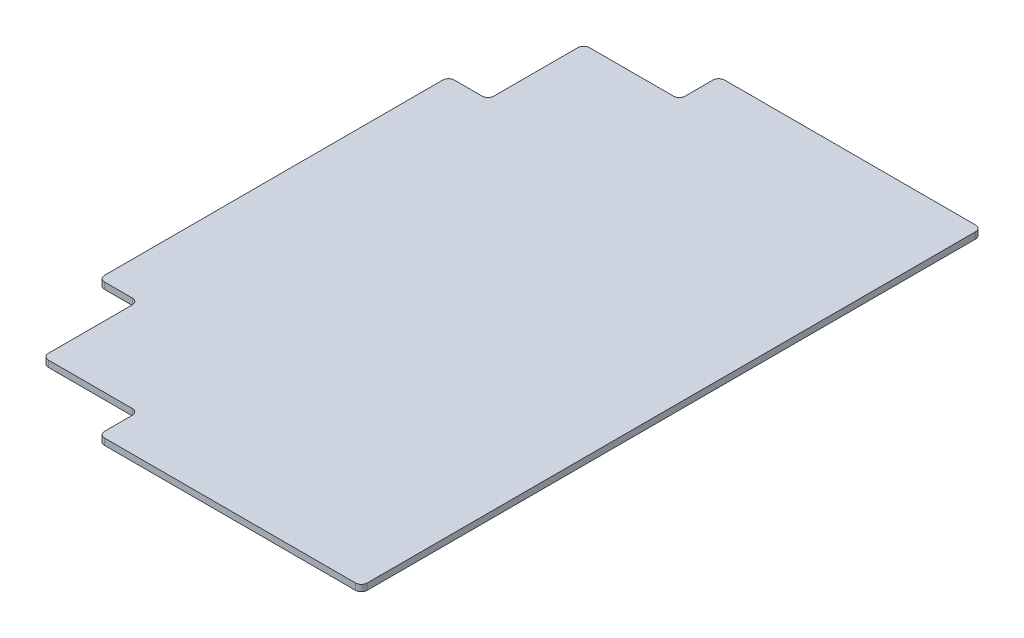
SolidWorks part; units mm, degrees
ref_plane "Front Plane" through (0, 0, 0) normal (0, 0, 1) x (1, 0, 0)
ref_plane "Top Plane" through (0, 0, 0) normal (0, 1, 0) x (1, 0, 0)
ref_plane "Right Plane" through (0, 0, 0) normal (1, 0, 0) x (0, 0, -1)
sketch "Sketch1" plane through (0, 0, 0) normal (0, 1, 0) x (1, 0, 0)
  line L1 (0, 0) -> (190.5, 0)
  line L2 (0, 0) -> (0, 304.8)
  line L3 (0, 304.8) -> (190.5, 304.8)
  line L4 (190.5, 0) -> (190.5, 304.8)
  dimension "D1" = 304.8
  dimension "D2" = 190.5
extrude "Boss-Extrude1" add sketch "Sketch1" along normal blind 2.7781
sketch "Sketch2" plane through (0, 2.7781, 0) normal (0, 1, 0) x (1, 0, 0)
  line L0 (190.5, 0) -> (190.5, 304.8) construction
  line L1 (0, 0) -> (190.5, 0)
  line L2 (0, 0) -> (0, 17.78)
  line L3 (0, 17.78) -> (190.5, 17.78)
  line L4 (190.5, 0) -> (190.5, 17.78)
  line L6 (0, 304.8) -> (190.5, 304.8)
  line L7 (0, 304.8) -> (0, 287.02)
  line L8 (0, 287.02) -> (190.5, 287.02)
  line L9 (190.5, 304.8) -> (190.5, 287.02)
  dimension "D1" = 17.78
  dimension "D2" = 17.78
extrude "Cut-Extrude1" cut sketch "Sketch2" against normal through all
sketch "Sketch3" plane through (0, 2.7781, 0) normal (0, 1, 0) x (1, 0, 0)
  line L0 (190.5, 17.78) -> (0, 17.78) construction
  line L1 (0, 287.02) -> (17.78, 287.02)
  line L2 (0, 287.02) -> (0, 17.78)
  line L3 (0, 17.78) -> (17.78, 17.78)
  line L4 (17.78, 287.02) -> (17.78, 17.78)
  dimension "D1" = 17.78
extrude "Cut-Extrude2" cut sketch "Sketch3" against normal through all
sketch "Sketch4" plane through (0, 2.7781, 0) normal (0, 1, 0) x (1, 0, 0)
  line L0 (17.78, 287.02) -> (76.454, 287.02)
  line L1 (17.78, 287.02) -> (190.5, 287.02) construction
  line L2 (76.454, 287.02) -> (76.454, 269.875)
  line L3 (76.454, 269.875) -> (34.925, 269.875)
  line L4 (34.925, 269.875) -> (34.925, 228.346)
  line L5 (34.925, 228.346) -> (17.78, 228.346)
  line L6 (17.78, 17.78) -> (17.78, 287.02) construction
  line L7 (17.78, 228.346) -> (17.78, 287.02)
  line L8 (17.78, 17.78) -> (76.454, 17.78)
  line L9 (190.5, 17.78) -> (17.78, 17.78) construction
  line L10 (76.454, 17.78) -> (76.454, 34.925)
  line L11 (76.454, 34.925) -> (34.925, 34.925)
  line L12 (34.925, 34.925) -> (34.925, 76.454)
  line L13 (34.925, 76.454) -> (17.78, 76.454)
  line L14 (17.78, 76.454) -> (17.78, 17.78)
  dimension "D2" = 58.674
  dimension "D3" = 17.145
extrude "Cut-Extrude3" cut sketch "Sketch4" against normal through all
fillet "Fillet1" radius 2.54 12 edges at (190.5, 1.3891, -287.02) (190.5, 1.3891, -17.78) (76.454, 1.3891, -17.78) (76.454, 1.3891, -34.925) (34.925, 1.3891, -34.925) (34.925, 1.3891, -76.454) (17.78, 1.3891, -76.454) (17.78, 1.3891, -228.346) (76.454, 1.3891, -287.02) (76.454, 1.3891, -269.875) (34.925, 1.3891, -269.875) (34.925, 1.3891, -228.346)
